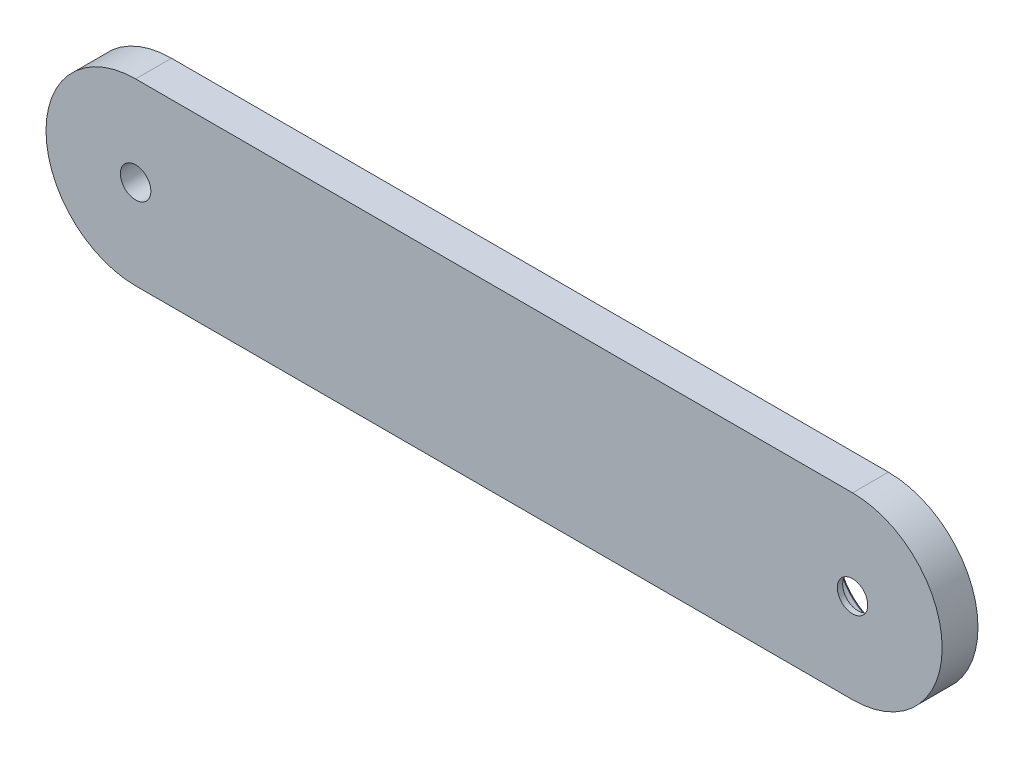
SolidWorks part; units mm, degrees
ref_plane "Front Plane" through (0, 0, 0) normal (0, 0, 1) x (1, 0, 0)
ref_plane "Top Plane" through (0, 0, 0) normal (0, 1, 0) x (1, 0, 0)
ref_plane "Right Plane" through (0, 0, 0) normal (1, 0, 0) x (0, 0, -1)
sketch "Sketch4" plane through (0, 0, 0) normal (0, 0, 1) x (1, 0, 0)
  line L0 (-60, 15) -> (60, 15)
  line L1 (60, -15) -> (-60, -15)
  line L2 (-60, 0) -> (60, 0) construction
  arc A0 (60, 15) -> (60, -15) centre (60, 0) cw
  arc A1 (-60, -15) -> (-60, 15) centre (-60, 0) cw
  dimension "D2" = 15
  dimension "D1" = 120
extrude "Boss-Extrude1" add sketch "Sketch4" along normal blind 6
sketch "Sketch9" plane through (0, 0, 0) normal (0, 0, -1) x (-1, 0, 0)
  circle A0 centre (-60, 0) radius 7.975
  dimension "D1" = 15.95
extrude "Cut-Extrude5" cut sketch "Sketch9" against normal blind 5.1
sketch "Sketch10" plane through (0, 0, 5.1) normal (0, 0, -1) x (-1, 0, 0)
  circle A0 centre (-60, 0) radius 2.55
  dimension "D1" = 5.1
extrude "Cut-Extrude6" cut sketch "Sketch10" against normal through all
sketch "Sketch11" plane through (0, 0, 0) normal (0, 0, -1) x (-1, 0, 0)
  circle A0 centre (60, 0) radius 2.55
  dimension "D1" = 5.1
extrude "Cut-Extrude7" cut sketch "Sketch11" against normal through all
chamfer "Chamfer1" distance 0.5 angle 45 1 edges at (52.025, 0, 0)
